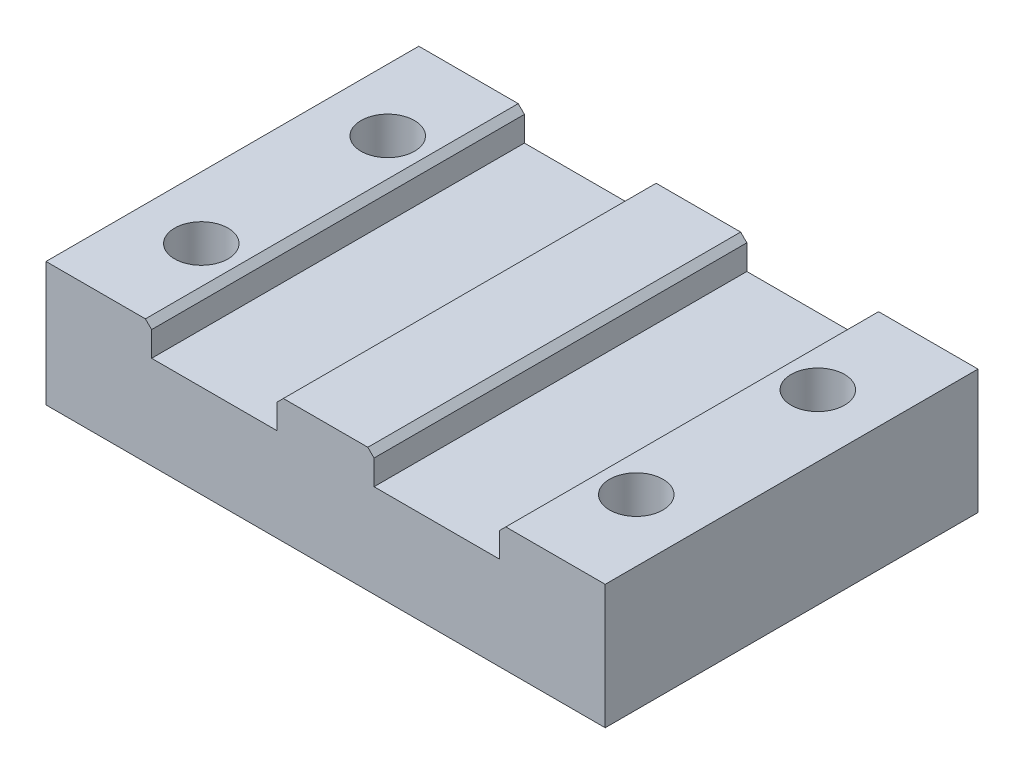
SolidWorks part; units mm, degrees
ref_plane "Спереди" through (0, 0, 0) normal (0, 0, 1) x (1, 0, 0)
ref_plane "Сверху" through (0, 0, 0) normal (0, 1, 0) x (1, 0, 0)
ref_plane "Справа" through (0, 0, 0) normal (1, 0, 0) x (0, 0, -1)
sketch "Sketch1" plane through (0, 0, 0) normal (0, 1, 0) x (1, 0, 0)
  line L1 (45, -30) -> (-45, -30)
  line L2 (45, -30) -> (45, 30)
  line L3 (45, 30) -> (-45, 30)
  line L4 (-45, -30) -> (-45, 30)
  line L5 (45, -30) -> (-45, 30) construction
  line L6 (45, 30) -> (-45, -30) construction
  point P0 (0, 0)
  dimension "D1" = 90
  dimension "D2" = 60
extrude "Boss-Extrude1" add sketch "Sketch1" along normal blind 20
sketch "Sketch2" plane through (0, 0, 30) normal (0, 0, 1) x (1, 0, 0)
  line L0 (-45, 20) -> (45, 20) construction
  line L1 (28, 25) -> (-28, 25)
  line L2 (28, 25) -> (28, 15)
  line L3 (28, 15) -> (-28, 15) construction
  line L4 (-28, 25) -> (-28, 15)
  line L5 (28, 25) -> (-28, 15) construction
  line L6 (28, 15) -> (-28, 25) construction
  line L7 (28, 15) -> (7.8, 15)
  line L8 (7.8, 15) -> (7.8, 20)
  line L9 (7.8, 20) -> (-7.8, 20)
  line L10 (-7.8, 20) -> (-7.8, 15)
  line L11 (-7.8, 15) -> (-28, 15)
  point P0 (0, 20)
  dimension "D1" = 56
  dimension "D2" = 10
  dimension "D3" = 20.2
  dimension "D4" = 15.6
extrude "Cut-Extrude1" cut sketch "Sketch2" against normal through all
sketch "Sketch3" plane through (0, 0, 0) normal (0, -1, 0) x (1, 0, 0)
  line L1 (-35, -15) -> (35, -15) construction
  line L2 (-35, -15) -> (-35, 15) construction
  line L3 (-35, 15) -> (35, 15) construction
  line L4 (35, -15) -> (35, 15) construction
  line L5 (-35, -15) -> (35, 15) construction
  line L6 (-35, 15) -> (35, -15) construction
  circle A0 centre (-35, 15) radius 4.3
  circle A1 centre (-35, -15) radius 4.3
  circle A2 centre (35, -14.2173) radius 4.3
  circle A3 centre (35, 15) radius 4.3
  point P0 (0, 0)
  dimension "D3" = 8.6
  dimension "D1" = 30
  dimension "D2" = 70
extrude "Cut-Extrude2" cut sketch "Sketch3" against normal through all
sketch "Sketch4" plane through (0, 0, 0) normal (0, -1, 0) x (1, 0, 0)
  circle A0 centre (35, 15) radius 8.8
  circle A1 centre (35, -14.2173) radius 8.8
  circle A2 centre (-35, 15) radius 8.8
  circle A3 centre (-35, -15) radius 8.8
  dimension "D1" = 17.6
extrude "Cut-Extrude3" cut sketch "Sketch4" against normal blind 10
chamfer "Chamfer1" distance 1 angle 45 4 edges at (-28, 20, 0) (28, 20, 0) (-7.8, 20, 0) (7.8, 20, 0)
